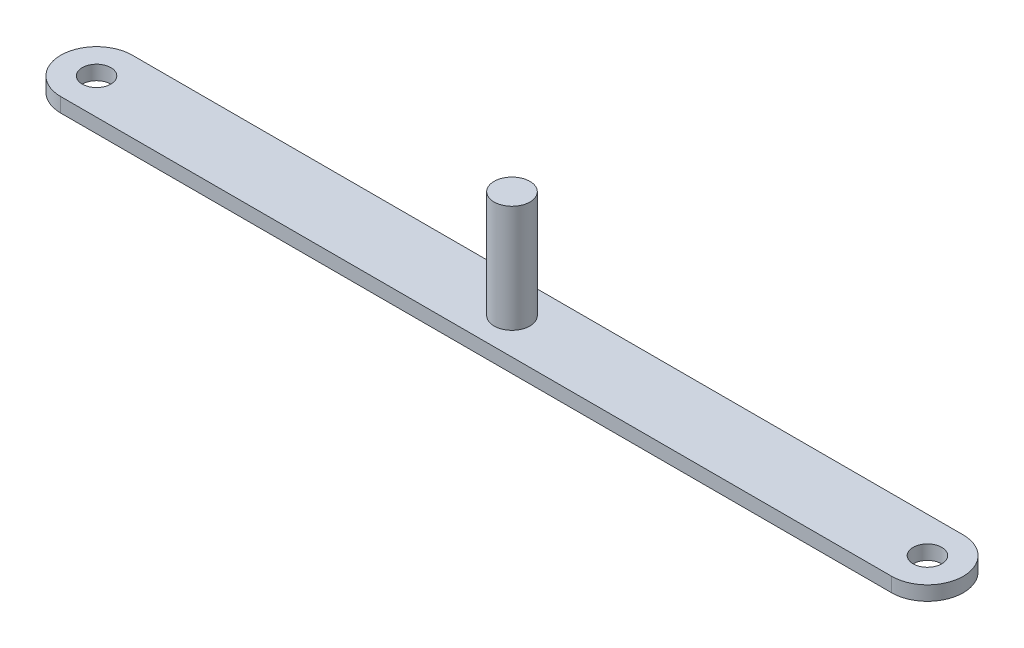
SolidWorks part; units mm, degrees
ref_plane "Front Plane" through (0, 0, 0) normal (0, 0, 1) x (1, 0, 0)
ref_plane "Top Plane" through (0, 0, 0) normal (0, 1, 0) x (1, 0, 0)
ref_plane "Right Plane" through (0, 0, 0) normal (1, 0, 0) x (0, 0, -1)
sketch "Sketch1" plane through (0, 0, 0) normal (0, 1, 0) x (1, 0, 0)
  line L0 (-58, 0) -> (58, 0) construction
  line L1 (-58, 5) -> (58, 5)
  line L2 (-58, -5) -> (58, -5)
  arc A0 (-58, 5) -> (-58, -5) centre (-58, 0) ccw
  arc A1 (58, -5) -> (58, 5) centre (58, 0) ccw
  circle A2 centre (-58, 0) radius 2
  circle A3 centre (58, 0) radius 2
  point P2 (0, 0)
  dimension "D3" = 4
  dimension "D4" = 4
  dimension "D1" = 10
  dimension "D2" = 116
extrude "Boss-Extrude1" add sketch "Sketch1" along normal blind 2
sketch "Sketch2" plane through (0, 2, 0) normal (0, 1, 0) x (1, 0, 0)
  circle A0 centre (0, 0) radius 2.5
  dimension "D1" = 5
extrude "Boss-Extrude2" add sketch "Sketch2" along normal blind 15
